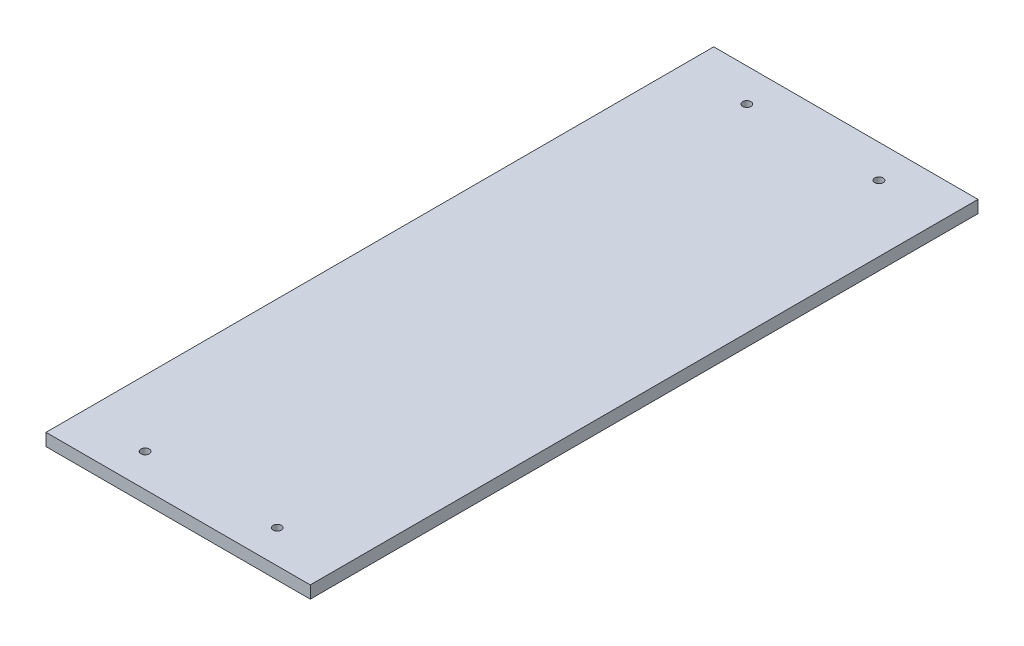
SolidWorks part; units mm, degrees
material "Balsa"
ref_plane "Front Plane" through (0, 0, 0) normal (0, 0, 1) x (1, 0, 0)
ref_plane "Top Plane" through (0, 0, 0) normal (0, 1, 0) x (1, 0, 0)
ref_plane "Right Plane" through (0, 0, 0) normal (1, 0, 0) x (0, 0, -1)
sketch "Sketch1" plane through (0, 0, 0) normal (0, 1, 0) x (1, 0, 0)
  line L0 (-152.4, 304.8) -> (152.4, 304.8) construction
  line L1 (152.4, 304.8) -> (152.4, -304.8) construction
  line L2 (0, 304.8) -> (0, 0) construction
  line L3 (0, 0) -> (152.4, 0) construction
  dimension "Width" = 304.8
  dimension "Length" = 609.6
sketch "Sketch2" plane through (0, 0, 0) normal (1, 0, 0) x (0, 0, -1)
  line L0 (304.8, 0) -> (304.8, -9.525) construction
  dimension "Thk" = 9.525
sketch "Sketch3" plane through (0, 0, 0) normal (0, 1, 0) x (1, 0, 0)
  line L1 (-152.4, 304.8) -> (152.4, 304.8)
  line L2 (-152.4, 304.8) -> (-152.4, -304.8)
  line L3 (-152.4, -304.8) -> (152.4, -304.8)
  line L4 (152.4, 304.8) -> (152.4, -304.8)
extrude "Boss-Extrude1" add sketch "Sketch3" against normal up to vertex (9.525 mm away) up to point (0, -9.525, -304.8)
sketch "Sketch4" plane through (0, 0, 0) normal (0, 1, 0) x (1, 0, 0)
  line L0 (152.4, -304.8) -> (152.4, 304.8) construction
  line L1 (-152.4, 304.8) -> (152.4, 304.8)
  line L2 (-152.4, 304.8) -> (-152.4, 208.661)
  line L3 (-120.245, 208.661) -> (120.245, 208.661)
  line L4 (152.4, 304.8) -> (152.4, 208.661)
  line L5 (-152.4, -304.8) -> (152.4, -304.8) construction
  line L6 (0, 0) -> (0, 208.661) construction
  line L8 (-152.4, 208.661) -> (-152.4, -304.8)
  line L9 (-152.4, -304.8) -> (-120.245, -304.8)
  line L10 (-120.245, 208.661) -> (-120.245, -304.8)
  line L11 (152.4, 208.661) -> (152.4, -304.8)
  line L12 (120.245, 208.661) -> (120.245, -304.8)
  line L13 (152.4, -304.8) -> (120.245, -304.8)
  dimension "D1" = 513.461
  dimension "D2" = 32.155
  dimension "D3" = 32.155
extrude "Cut-Extrude1" cut sketch "Sketch4" against normal blind 15.24 contours L2 L8 L9 L10 L3 L12 L13 L11 L4 L1
sketch "Sketch5" plane through (0, 0, 0) normal (0, 1, 0) x (1, 0, 0)
  line L1 (-50.8, -109.22) -> (50.8, -109.22)
  line L2 (-57.15, -102.87) -> (-57.15, -20.32)
  line L3 (-50.8, -13.97) -> (50.8, -13.97)
  line L4 (57.15, -102.87) -> (57.15, -20.32)
  line L5 (-57.15, -109.22) -> (57.15, -13.97) construction
  line L6 (-57.15, -13.97) -> (57.15, -109.22) construction
  arc A0 (-50.8, -109.22) -> (-57.15, -102.87) centre (-50.8, -102.87) cw
  arc A1 (50.8, -109.22) -> (57.15, -102.87) centre (50.8, -102.87) ccw
  arc A2 (50.8, -13.97) -> (57.15, -20.32) centre (50.8, -20.32) cw
  arc A3 (-57.15, -20.32) -> (-50.8, -13.97) centre (-50.8, -20.32) cw
  point P0 (0, -61.595)
  dimension "D4" = 6.35
  dimension "D1" = 95.25
  dimension "D2" = 61.595
  dimension "D3" = 114.3
extrude "Cut-Extrude2" [suppressed] cut sketch "Sketch5" against normal blind 12.7
sketch "Sketch9" plane through (0, -9.525, 0) normal (0, -1, 0) x (-1, 0, 0)
  line L0 (120.1778, 208.661) -> (-120.245, 208.661) construction
  line L1 (120.245, 208.661) -> (-120.245, 208.661) construction
  line L3 (-120.245, 208.661) -> (-120.245, -304.8) construction
  line L4 (120.245, -304.8) -> (-120.245, -304.8) construction
  line L5 (-120.245, -304.8) -> (-120.245, -48.0695) construction
  line L6 (-120.245, -48.0695) -> (120.245, -48.0695) construction
  line L7 (50.7664, 208.661) -> (-0.0336, 208.661) construction
  line L8 (-0.0336, 208.661) -> (-50.8336, 208.661) construction
  line L9 (50.7664, 208.661) -> (50.7664, 183.261) construction
  line L10 (50.7664, 183.261) -> (-50.8336, 183.261) construction
  line L11 (-50.8336, 183.261) -> (-50.8336, 208.661) construction
  line L13 (120.245, 208.661) -> (120.245, -304.8) construction
  circle A0 centre (-50.8336, 183.261) radius 3.2258
  circle A2 centre (50.7664, 183.261) radius 3.2258
  circle A5 centre (50.7664, -279.4) radius 3.2258
  circle A6 centre (-50.8336, -279.4) radius 3.2258
  point P5 (50.7664, 183.261)
  point P17 (0, 0)
  point P23 (120.2114, 208.661)
  point P24 (-97.6961, 208.661)
  point P25 (0, 0)
  point P26 (-120.245, 208.661)
  point P29 (120.245, -48.0695)
  point P32 (-120.245, -48.0695)
  point P33 (-120.245, -304.8)
  point P35 (0, -304.8)
  point P36 (0, 0)
  dimension "D3" = 25.4
  dimension "D1" = 6.4516
  dimension "D5" = 50.8336
  dimension "D2" = 50.8
  dimension "D4" = 50.8
extrude "Cut-Extrude3" cut sketch "Sketch9" against normal through all
sketch "Sketch10" plane through (0, -9.525, 0) normal (0, -1, 0) x (1, 0, 0)
  line L0 (-120.245, -208.661) -> (120.245, -208.661) construction
  line L1 (-101.6, -208.661) -> (101.6, -208.661)
  line L2 (-101.6, -208.661) -> (-101.6, 304.8)
  line L3 (-101.6, 304.8) -> (101.6, 304.8)
  line L4 (101.6, -208.661) -> (101.6, 304.8)
  line L5 (-120.245, 304.8) -> (120.245, 304.8) construction
  line L6 (-101.6, 0) -> (101.6, 0) construction
  line L8 (-120.245, -208.661) -> (120.245, -208.661)
  line L9 (-120.245, -208.661) -> (-120.245, 304.8)
  line L10 (-120.245, 304.8) -> (120.245, 304.8)
  line L11 (120.245, -208.661) -> (120.245, 304.8)
  line M6 (-120.245, -208.661) -> (120.245, -208.661)
  line M7 (120.245, -208.661) -> (120.245, 304.8)
  line M8 (120.245, 304.8) -> (-120.245, 304.8)
  line M9 (-120.245, 304.8) -> (-120.245, -208.661)
  dimension "D1" = 203.2
extrude "Cut-Extrude4" cut sketch "Sketch10" against normal blind 41.656 contours L4 M6 M7 M8 | L2 M6 M8 M9
